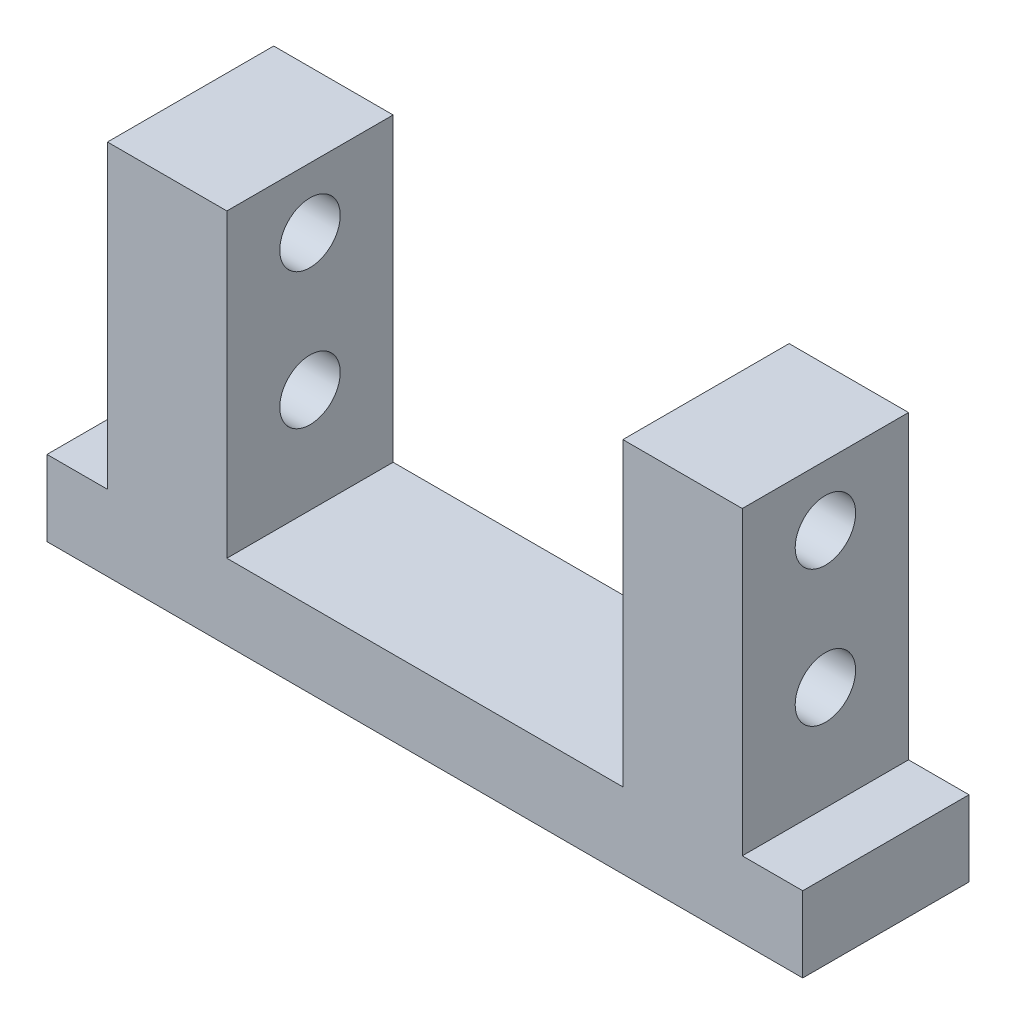
SolidWorks part; units mm, degrees
ref_plane "Front Plane" through (0, 0, 0) normal (0, 0, 1) x (1, 0, 0)
ref_plane "Top Plane" through (0, 0, 0) normal (0, 1, 0) x (1, 0, 0)
ref_plane "Right Plane" through (0, 0, 0) normal (1, 0, 0) x (0, 0, -1)
sketch "Sketch1" plane through (0, 0, 0) normal (0, 1, 0) x (1, 0, 0)
  line L1 (-50, -11) -> (50, -11)
  line L2 (-50, -11) -> (-50, 11)
  line L3 (-50, 11) -> (50, 11)
  line L4 (50, -11) -> (50, 11)
  line L5 (-50, -11) -> (50, 11) construction
  line L6 (-50, 11) -> (50, -11) construction
  point P0 (0, 0)
  dimension "D1" = 100
  dimension "D2" = 22
extrude "Boss-Extrude1" add sketch "Sketch1" along normal blind 10
sketch "Sketch2" plane through (0, 10, 0) normal (0, 1, 0) x (1, 0, 0)
  line L0 (50, 11) -> (-50, 11) construction
  line L1 (42, -11) -> (-42, -11)
  line L2 (42, -11) -> (42, 11)
  line L3 (42, 11) -> (-42, 11)
  line L4 (-42, -11) -> (-42, 11)
  line L5 (42, -11) -> (-42, 11) construction
  line L6 (42, 11) -> (-42, -11) construction
  point P0 (0, 0)
  dimension "D1" = 84
extrude "Boss-Extrude2" add sketch "Sketch2" along normal blind 39.8
sketch "Sketch3" plane through (0, 49.8, 0) normal (0, 1, 0) x (1, 0, 0)
  line L0 (42, 11) -> (-42, 11) construction
  line L1 (26.2, -11) -> (-26.2, -11)
  line L2 (26.2, -11) -> (26.2, 11)
  line L3 (26.2, 11) -> (-26.2, 11)
  line L4 (-26.2, -11) -> (-26.2, 11)
  line L5 (26.2, -11) -> (-26.2, 11) construction
  line L6 (26.2, 11) -> (-26.2, -11) construction
  point P0 (0, 0)
  dimension "D1" = 52.4
extrude "Cut-Extrude1" cut sketch "Sketch3" against normal blind 39.8
sketch "Sketch4" plane through (-42, 0, 0) normal (-1, 0, 0) x (0, 0, 1)
  line L0 (-11, 49.8) -> (11, 49.8) construction
  circle A0 centre (0, 41.8) radius 4
  circle A1 centre (0, 23.8) radius 4
  dimension "D3" = 8
  dimension "D4" = 8
  dimension "D1" = 8
  dimension "D2" = 26
extrude "Cut-Extrude2" cut sketch "Sketch4" against normal through all
